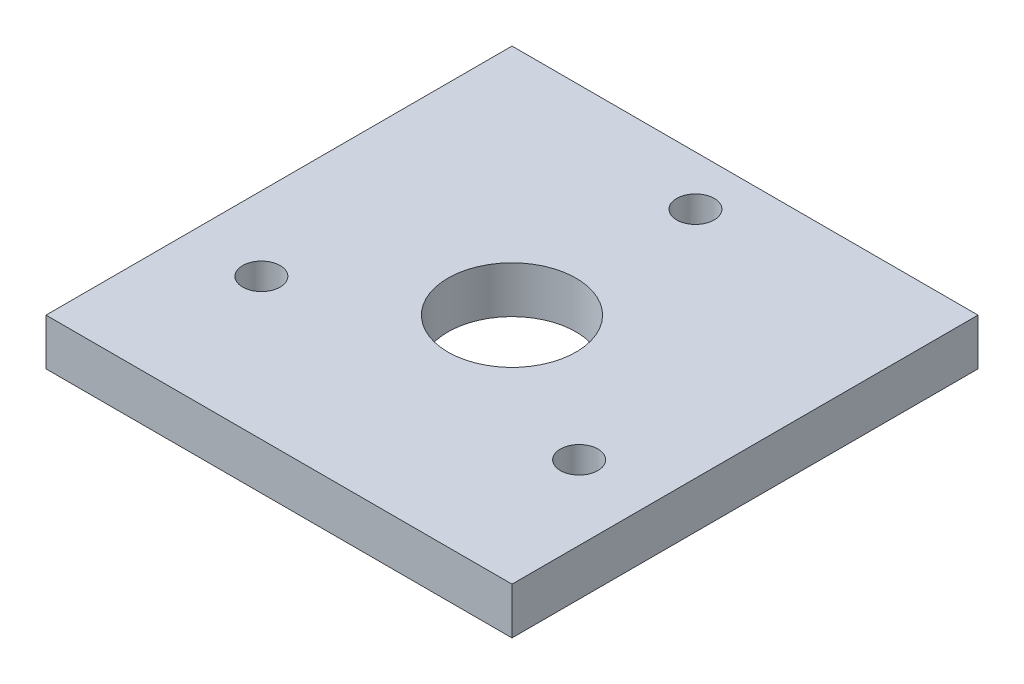
SolidWorks part; units mm, degrees
ref_plane "Front" through (0, 0, 0) normal (0, 0, 1) x (1, 0, 0)
ref_plane "Top" through (0, 0, 0) normal (0, 1, 0) x (1, 0, 0)
ref_plane "Right" through (0, 0, 0) normal (1, 0, 0) x (0, 0, -1)
sketch "Sketch1" plane through (0, 0, 0) normal (0, 1, 0) x (1, 0, 0)
  line L1 (31.75, -31.75) -> (-31.75, -31.75)
  line L2 (31.75, -31.75) -> (31.75, 31.75)
  line L3 (31.75, 31.75) -> (-31.75, 31.75)
  line L4 (-31.75, -31.75) -> (-31.75, 31.75)
  line L5 (31.75, -31.75) -> (-31.75, 31.75) construction
  line L6 (31.75, 31.75) -> (-31.75, -31.75) construction
  circle A0 centre (0, 25) radius 2.5527
  circle A1 centre (0, 0) radius 8.7312
  circle A2 centre (21.6506, -12.5) radius 2.5527
  circle A3 centre (-21.6506, -12.5) radius 2.5527
  point P1 (0, 0)
  point P16 (0, 0)
  dimension "D2" = 17.4625
  dimension "D3" = 5.1054
  dimension "D1" = 63.5
  dimension "D4" = 25
  dimension "D5" = 3
extrude "Boss-Extrude1" add sketch "Sketch1" along normal blind 6.35 contours L4 L3 L2 L1
